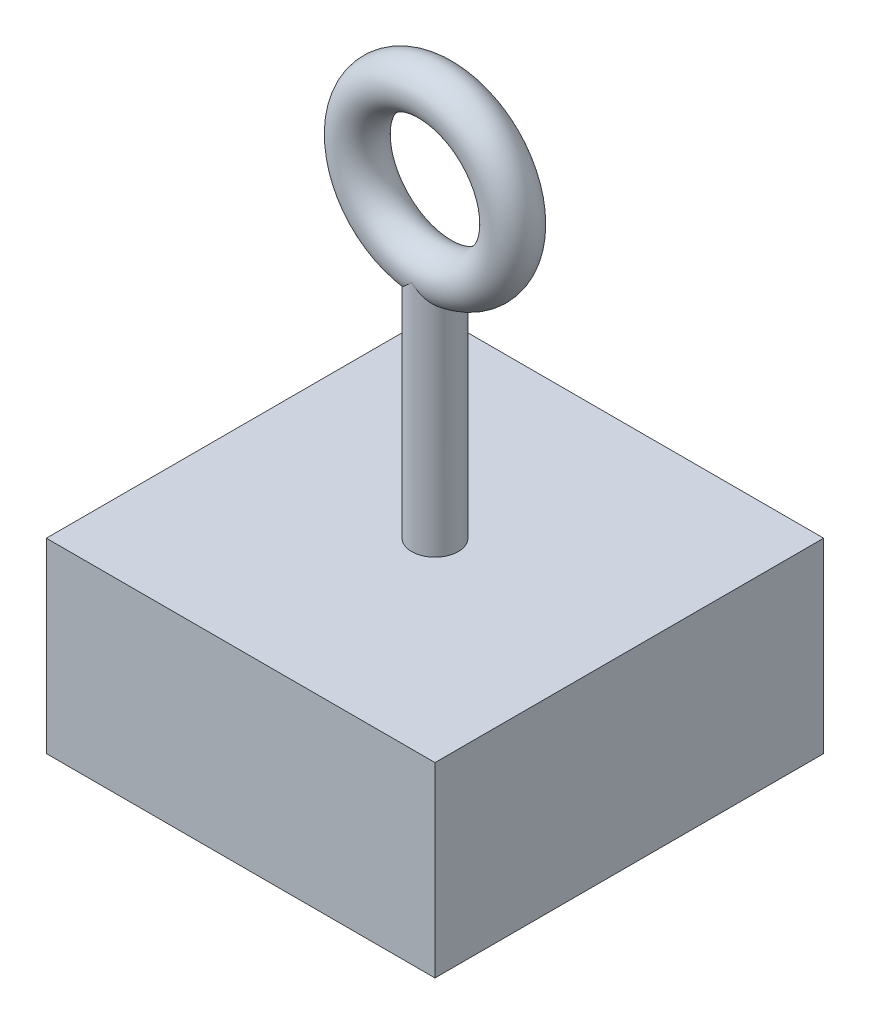
SolidWorks part; units mm, degrees
ref_plane "Front Plane" through (0, 0, 0) normal (0, 0, 1) x (1, 0, 0)
ref_plane "Top Plane" through (0, 0, 0) normal (0, 1, 0) x (1, 0, 0)
ref_plane "Right Plane" through (0, 0, 0) normal (1, 0, 0) x (0, 0, -1)
sketch "Sketch1" plane through (0, 0, 0) normal (0, 1, 0) x (1, 0, 0)
  line L1 (12.5, -12.5) -> (-12.5, -12.5)
  line L2 (12.5, -12.5) -> (12.5, 12.5)
  line L3 (12.5, 12.5) -> (-12.5, 12.5)
  line L4 (-12.5, -12.5) -> (-12.5, 12.5)
  line L5 (12.5, -12.5) -> (-12.5, 12.5) construction
  line L6 (12.5, 12.5) -> (-12.5, -12.5) construction
  point P0 (0, 0)
  dimension "D1" = 25
  dimension "D2" = 25
extrude "Boss-Extrude1" add sketch "Sketch1" along normal blind 12
sketch "Sketch2" plane through (0, 12, 0) normal (0, 1, 0) x (1, 0, 0)
  circle A0 centre (0, 0) radius 1.5
  dimension "D1" = 3
extrude "Boss-Extrude2" add sketch "Sketch2" along normal blind 15
ref_plane "Plane1" through (0, 32, 0) normal (0, 1, 0) x (1, 0, 0)
ref_axis "Axis1" through (0, 32, -13.75) along (0, 0, 1)
sketch "Sketch3" plane through (0, 32, 0) normal (0, 1, 0) x (1, 0, 0)
  circle A0 centre (-5, 0) radius 1.5
  point P2 (0, 0)
  dimension "D1" = 3
  dimension "D2" = 5
revolve "Revolve1" add sketch "Sketch3" angle 360 about axis through (0, 32, -13.75) along (0, 0, 1)
equation "\"12mmn\"=0.1"
